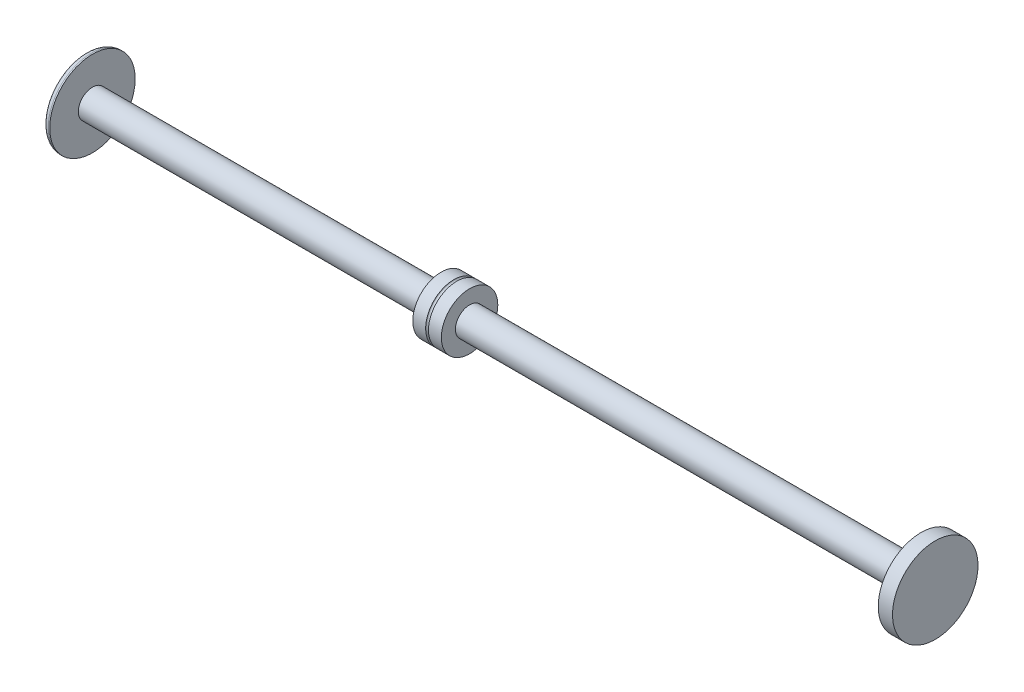
SolidWorks part; units mm, degrees
material "Plain Carbon Steel"
ref_plane "Front Plane" through (0, 0, 0) normal (0, 0, 1) x (1, 0, 0)
ref_plane "Top Plane" through (0, 0, 0) normal (0, 1, 0) x (1, 0, 0)
ref_plane "Right Plane" through (0, 0, 0) normal (1, 0, 0) x (0, 0, -1)
sketch "Sketch2" plane through (25.4, 0, -190.1998) normal (0, 0, 1) x (1, 0, 0)
  line L3 (-10.16, 1439.0865) -> (114.3, 1439.0865)
  line L4 (-91.44, 1439.0865) -> (-101.6, 1439.0865)
  line L5 (-101.6, 1439.0865) -> (-177.8, 1439.0865)
  line L6 (-91.44, 1439.0865) -> (-101.6, 1439.0865)
  line L7 (-101.6, 1439.0865) -> (-177.8, 1439.0865)
  line L8 (-10.16, 1445.3857) -> (-10.16, 1420.1889) construction
  line L9 (114.3, 1493.1123) -> (114.3, 1372.4623) construction
  line L10 (0, 1432.7873) -> (-223.2442, 1432.7873) construction
  line L11 (0, 1449.2973) -> (0, 1416.2773) construction
  line L13 (-177.8, 1439.0865) -> (-177.8, 1451.7865)
  line L14 (-10.16, 1445.3349) -> (-10.16, 1439.0865)
  line L16 (-22.86, 1445.3349) -> (-22.86, 1439.0865)
  line L17 (-91.44, 1439.0865) -> (-22.86, 1439.0865)
  line L18 (-177.8, 1331.1638) -> (-177.8, 2028.051) construction
  line L19 (-10.16, 1445.3349) -> (-91.44, 1445.3349)
  line L20 (-10.16, 1445.3349) -> (-22.86, 1445.3349)
  line L21 (-177.8, 1451.7865) -> (-178.435, 1451.7865)
  line L22 (-180.975, 1449.2465) -> (-180.975, 1432.7873)
  line L23 (-180.975, 1432.7873) -> (196.85, 1432.7873)
  line L24 (196.85, 1432.7873) -> (196.85, 1451.7865)
  line L25 (196.85, 1451.7865) -> (190.5, 1451.7865)
  line L26 (190.5, 1451.7865) -> (190.5, 1439.0865)
  line L27 (190.5, 1439.0865) -> (114.3, 1439.0865)
  arc A0 (-178.435, 1451.7865) -> (-180.975, 1449.2465) centre (-178.435, 1449.2465) ccw
  dimension "D6" = 2.54
  dimension "D2" = 12.7
  dimension "D4" = 3.175
  dimension "D5" = 12.7
  dimension "D7" = 76.2
  dimension "D8" = 6.35
  dimension "D9" = 12.7
  dimension "D1" = 0.0508
  dimension "D3" = 0.0508
revolve "Revolve1" add sketch "Sketch2" angle 360 about L10
sketch "Sketch3" plane through (25.4, 0, -190.1998) normal (0, 0, 1) x (1, 0, 0)
  line L2 (-10.16, 1445.3349) -> (-22.86, 1445.3349) construction
  line L3 (-22.86, 1432.7873) -> (-10.16, 1432.7873) construction
  line L4 (-22.86, 1445.3349) -> (-22.86, 1420.2397) construction
  line L5 (-10.16, 1420.2397) -> (-10.16, 1445.3349) construction
  circle A0 centre (-16.51, 1445.3349) radius 0.635
  point P4 (-16.51, 1445.3349)
  dimension "D1" = 1.27
revolve "Cut-Revolve1" cut sketch "Sketch3" angle 360 about L3
